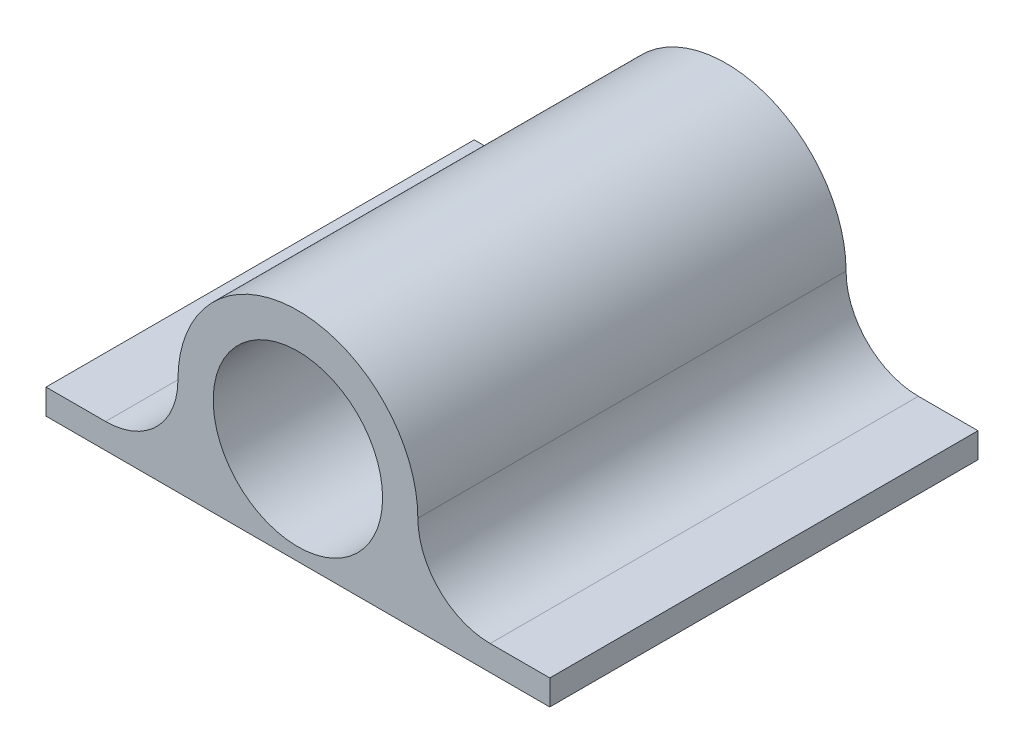
SolidWorks part; units mm, degrees
ref_plane "Front Plane" through (0, 0, 0) normal (0, 0, 1) x (1, 0, 0)
ref_plane "Top Plane" through (0, 0, 0) normal (0, 1, 0) x (1, 0, 0)
ref_plane "Right Plane" through (0, 0, 0) normal (1, 0, 0) x (0, 0, -1)
sketch "Sketch1" plane through (0, 0, 0) normal (0, 0, 1) x (1, 0, 0)
  line L0 (-9.6945, -3.6465) -> (-12.7, -3.6465)
  line L1 (12.7, -4.9165) -> (-12.7, -4.9165)
  line L2 (12.7, -4.9165) -> (12.7, -3.6465)
  line L3 (12.7, -3.6465) -> (9.6945, -3.6465)
  line L4 (-12.7, -4.9165) -> (-12.7, -3.6465)
  line L5 (12.7, -4.9165) -> (-12.7, -3.6465) construction
  line L6 (12.7, -3.6465) -> (-12.7, -4.9165) construction
  circle A0 centre (0, 0) radius 3.1115
  arc A2 (-6.048, 0) -> (6.048, 0) centre (0, 0) cw
  arc A3 (-6.048, 0) -> (-9.6945, -3.6465) centre (-9.6945, 0) cw
  arc A4 (6.048, 0) -> (9.6945, -3.6465) centre (9.6945, 0) ccw
  point P5 (0, -4.2815)
  dimension "D2" = 6.048
  dimension "D4" = 6.223
  dimension "D1" = 1.27
  dimension "D3" = 25.4
extrude "Boss-Extrude1" add sketch "Sketch1" along normal blind 20.32
sketch "Sketch2" plane through (0, 0, 0) normal (0, 0, -1) x (-1, 0, 0)
  line L5 (12.7, -4.9165) -> (12.7, -3.6465)
  line L6 (12.7, -3.6465) -> (9.6945, -3.6465)
  line L7 (-9.6945, -3.6465) -> (-12.7, -3.6465)
  line L8 (-12.7, -3.6465) -> (-12.7, -4.9165)
  line L9 (-12.7, -4.9165) -> (12.7, -4.9165)
  line L10 (12.7, -4.9165) -> (12.7, -3.6465)
  line L11 (12.7, -3.6465) -> (9.6945, -3.6465)
  line L12 (-9.6945, -3.6465) -> (-12.7, -3.6465)
  line L13 (-12.7, -3.6465) -> (-12.7, -4.9165)
  line L14 (-12.7, -4.9165) -> (12.7, -4.9165)
  circle A0 centre (0, 0) radius 1.905
  arc A3 (6.048, 0) -> (9.6945, -3.6465) centre (9.6945, 0) ccw
  arc A4 (6.048, 0) -> (-6.048, 0) centre (0, 0) ccw
  arc A5 (-9.6945, -3.6465) -> (-6.048, 0) centre (-9.6945, 0) ccw
  arc A6 (6.048, 0) -> (9.6945, -3.6465) centre (9.6945, 0) ccw
  arc A7 (6.048, 0) -> (-6.048, 0) centre (0, 0) ccw
  arc A8 (-9.6945, -3.6465) -> (-6.048, 0) centre (-9.6945, 0) ccw
  dimension "D2" = 3.81
  dimension "D1" = 0
extrude "Boss-Extrude2" add sketch "Sketch2" along normal blind 1.27
sketch "Sketch3" plane through (0, 0, 20.32) normal (0, 0, 1) x (1, 0, 0)
  circle A0 centre (0, 0) radius 4.27
  arc A1 (6.048, 0) -> (-6.048, 0) centre (0, 0) ccw construction
  dimension "D1" = 1.778
extrude "Cut-Extrude1" cut sketch "Sketch3" against normal blind 10.16
